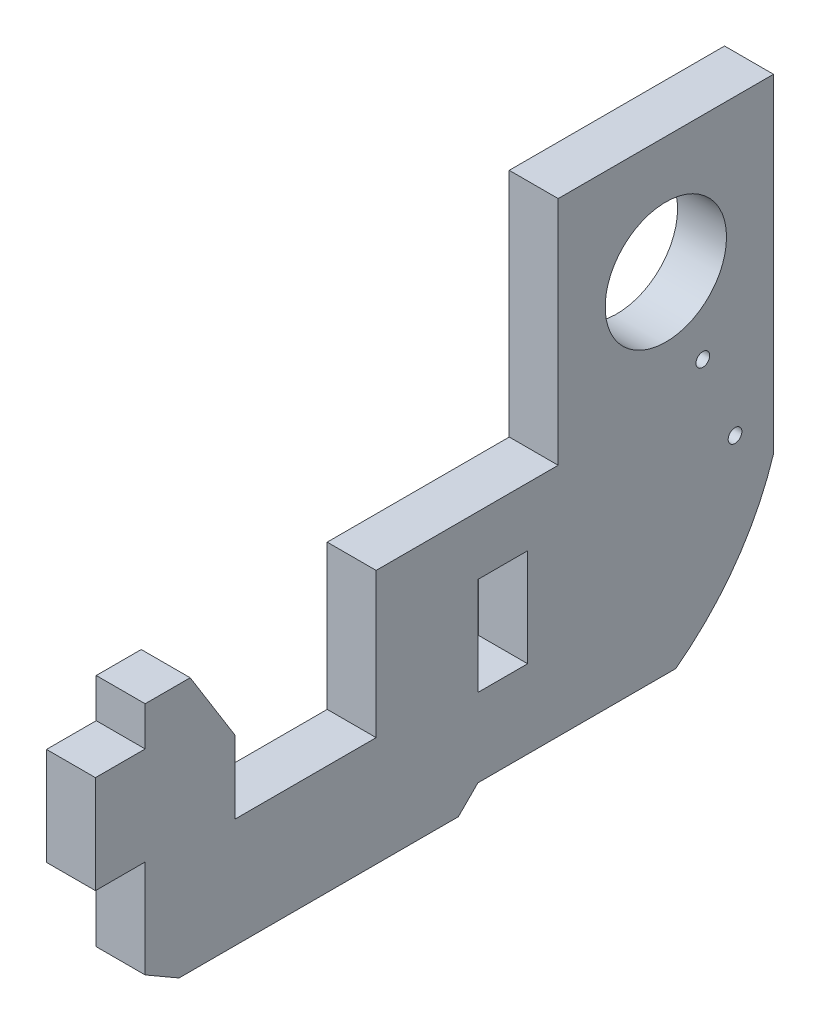
SolidWorks part; units mm, degrees
ref_plane "Front Plane" through (0, 0, 0) normal (0, 0, 1) x (1, 0, 0)
ref_plane "Top Plane" through (0, 0, 0) normal (0, 1, 0) x (1, 0, 0)
ref_plane "Right Plane" through (0, 0, 0) normal (1, 0, 0) x (0, 0, -1)
sketch "Sketch1" plane through (0, 0, 0) normal (1, 0, 0) x (0, 0, -1)
  line L0 (-6.985, 7.62) -> (6.985, 7.62)
  line L1 (-6.985, 7.62) -> (-6.985, -7.366)
  line L2 (-6.985, -7.366) -> (-18.796, -7.366)
  line L3 (-33.782, -7.366) -> (-33.782, -9.906)
  line L4 (-33.782, -9.906) -> (-37.0078, -9.906)
  line L5 (-37.0078, -9.906) -> (-37.0078, -16.256)
  line L6 (-37.0078, -16.256) -> (-33.782, -16.256)
  line L7 (-33.782, -16.256) -> (-33.782, -22.606)
  line L8 (-33.782, -22.606) -> (6.985, -22.606)
  line L9 (6.985, -22.606) -> (6.985, 7.62)
  line L10 (0, 0) -> (4.7958, -12.2087) construction
  line L11 (-18.796, -7.366) -> (-18.796, -16.764)
  line L12 (-12.192, -11.176) -> (-8.9662, -11.176)
  line L13 (-12.192, -11.176) -> (-12.192, -17.526)
  line L14 (-12.192, -17.526) -> (-8.9662, -17.526)
  line L15 (-8.9662, -11.176) -> (-8.9662, -17.526)
  line L16 (-12.192, -11.176) -> (-8.9662, -17.526) construction
  line L17 (-12.192, -17.526) -> (-8.9662, -11.176) construction
  line L18 (-18.796, -16.764) -> (-27.94, -16.764)
  line L19 (-27.94, -16.764) -> (-27.94, -7.366)
  line L20 (-27.94, -7.366) -> (-33.782, -7.366)
  circle A0 centre (0, 0) radius 3.937
  circle A3 centre (0, 0) radius 6.5659 construction
  circle A4 centre (0, 0) radius 12.2809 construction
  circle A5 centre (2.4006, -6.1113) radius 0.4445
  circle A6 centre (4.4901, -11.4307) radius 0.4445
  point P2 (-10.5791, -14.351)
  dimension "D11" = 3.2258
  dimension "D12" = 6.35
  dimension "D13" = 21.59
  dimension "D6" = 7.366
  dimension "D7" = 90
  dimension "D8" = 33.782
  dimension "D2" = 7.874
  dimension "D22" = 0.889
  dimension "D23" = 0.889
  dimension "D3" = 7.62
  dimension "D4" = 6.985
  dimension "D5" = 6.985
  dimension "D9" = 6.35
  dimension "D10" = 2.54
  dimension "D14" = 5.08
  dimension "D15" = 3.2258
  dimension "D16" = 5.842
  dimension "D17" = 9.144
  dimension "D18" = 9.398
  dimension "D21" = 6.35
extrude "Boss-Extrude1" add sketch "Sketch1" along normal blind 3.175
sketch "Sketch2" plane through (0, 0, 0) normal (-1, 0, 0) x (0, 0, 1)
  line L0 (13.462, -23.876) -> (31.5823, -23.876)
  line L1 (31.5823, -23.876) -> (33.782, -22.606)
  line L2 (13.462, -23.876) -> (12.192, -22.606)
  line L3 (33.782, -22.606) -> (-6.985, -22.606) construction
  line L4 (12.192, -22.606) -> (33.782, -22.606)
  dimension "D1" = 45
  dimension "D2" = 150
  dimension "D3" = 1.27
extrude "Boss-Extrude2" add sketch "Sketch2" against normal blind 3.175
sketch "Sketch3" plane through (3.175, 0, 0) normal (1, 0, 0) x (0, 0, -1)
  line L0 (-30.861, -7.366) -> (-27.94, -7.366)
  line L1 (-27.94, -7.366) -> (-33.782, -7.366) construction
  line L2 (-27.94, -7.366) -> (-27.94, -12.065)
  line L3 (-27.94, -16.764) -> (-27.94, -7.366) construction
  line L4 (-27.94, -12.065) -> (-30.861, -7.366)
  line L5 (6.985, -13.716) -> (6.985, -22.606)
  line L6 (6.985, -22.606) -> (6.985, 7.62) construction
  line L7 (6.985, -22.606) -> (0.635, -22.606)
  line L8 (-12.192, -22.606) -> (6.985, -22.606) construction
  arc A0 (6.985, -13.716) -> (0.635, -22.606) centre (-9.9585, -8.3264) cw
  dimension "D3" = 17.78
  dimension "D1" = 6.35
  dimension "D2" = 8.89
extrude "Cut-Extrude1" cut sketch "Sketch3" against normal through all
